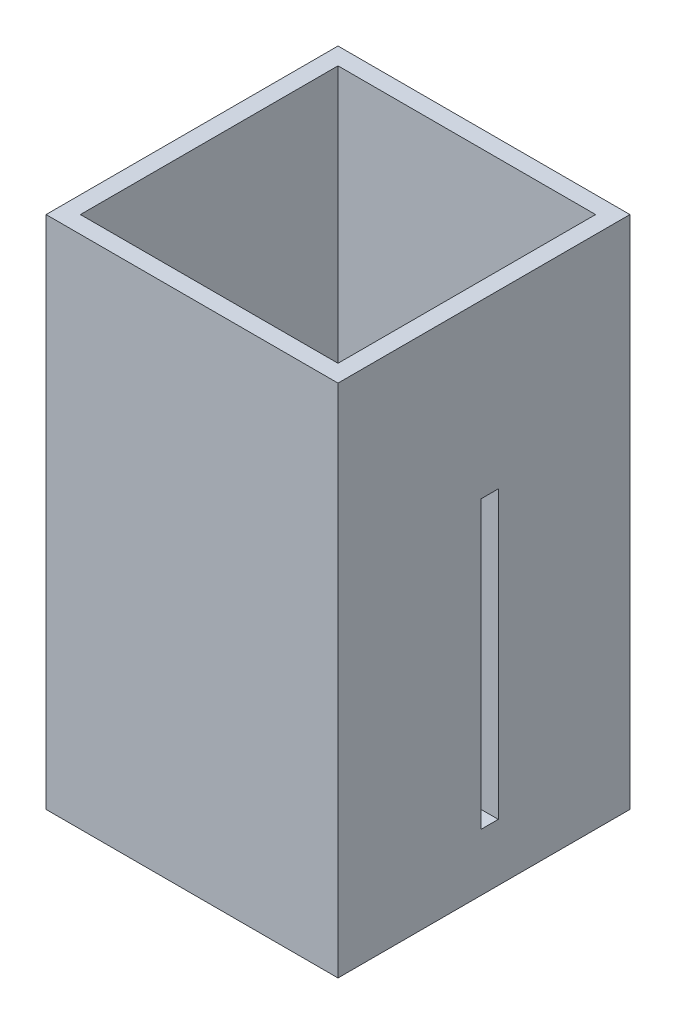
SolidWorks part; units mm, degrees
ref_plane "Front" through (0, 0, 0) normal (0, 0, 1) x (1, 0, 0)
ref_plane "Top" through (0, 0, 0) normal (0, 1, 0) x (1, 0, 0)
ref_plane "Right" through (0, 0, 0) normal (1, 0, 0) x (0, 0, -1)
sketch "Sketch1" plane through (0, 0, 0) normal (0, 1, 0) x (1, 0, 0)
  line L1 (-25.5, 25.5) -> (25.5, 25.5)
  line L2 (-25.5, 25.5) -> (-25.5, -25.5)
  line L3 (-25.5, -25.5) -> (25.5, -25.5)
  line L4 (25.5, 25.5) -> (25.5, -25.5)
  line L5 (-25.5, 25.5) -> (25.5, -25.5) construction
  line L6 (-25.5, -25.5) -> (25.5, 25.5) construction
  point P0 (0, 0)
  dimension "D1" = 51
  dimension "D2" = 51
extrude "Boss-Extrude1" add sketch "Sketch1" along normal blind 90
shell "Shell1" thickness 3
sketch "Sketch2" plane through (0, 0, 0) normal (1, 0, 0) x (0, 0, -1)
  line L0 (-25.5, 0) -> (25.5, 0) construction
  line L1 (2.5, 10) -> (-0.5, 10)
  line L2 (2.5, 10) -> (2.5, 60)
  line L3 (2.5, 60) -> (-0.5, 60)
  line L4 (-0.5, 10) -> (-0.5, 60)
  line L5 (25.5, 90) -> (25.5, 0) construction
  dimension "D1" = 10
  dimension "D2" = 23
  dimension "D3" = 50
  dimension "D4" = 3
extrude "Cut-Extrude1" cut sketch "Sketch2" against normal through all both and the other way through all
ref_plane "Plane1" through (0, 10, 0) normal (0, -1, 0) x (-1, 0, 0)
sketch "Sketch5" plane through (0, 10, 0) normal (0, -1, 0) x (-1, 0, 0)
  line L0 (22.5, -22.5) -> (-22.5, -22.5) construction
  circle A0 centre (0, -2.5) radius 15
  dimension "D1" = 20
extrude "Boss-Extrude3" add sketch "Sketch5" against normal blind 10 separate body
